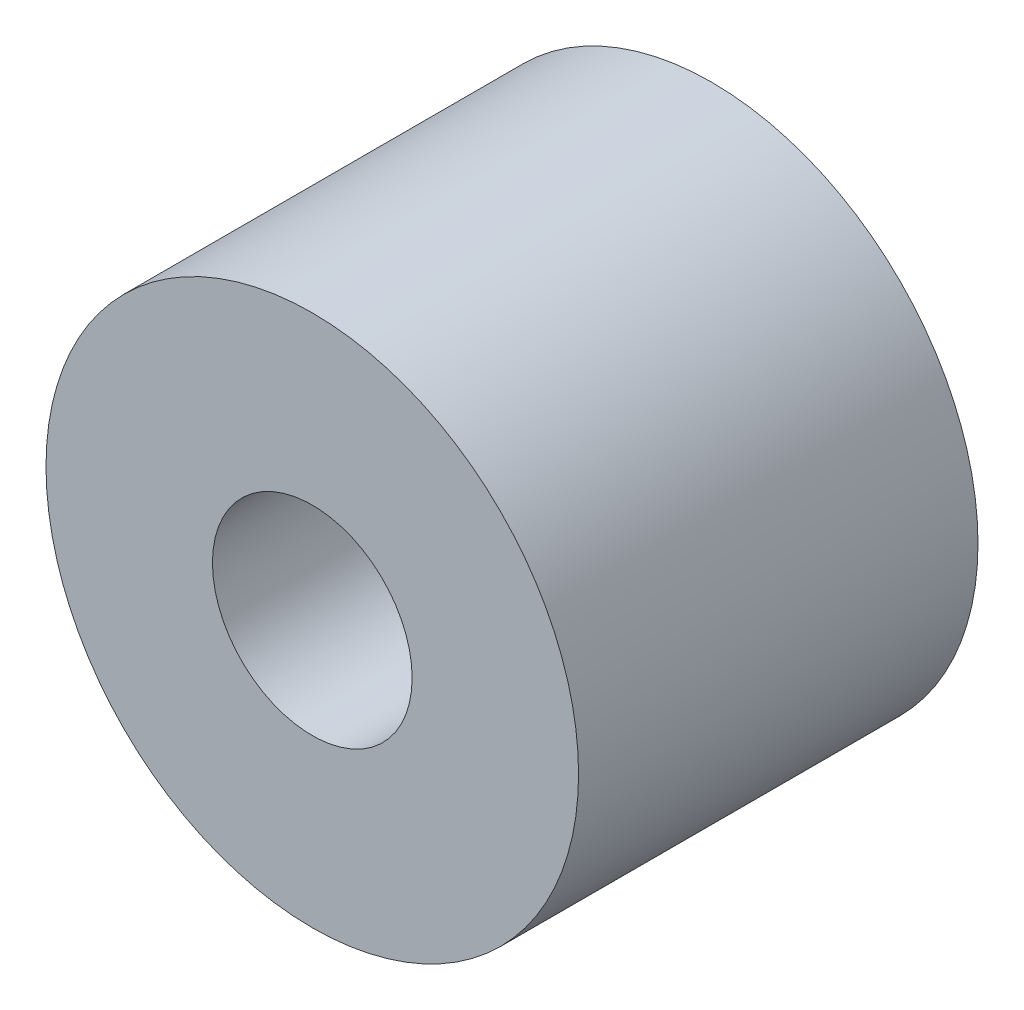
SolidWorks part; units mm, degrees
ref_plane "Front Plane" through (0, 0, 0) normal (0, 0, 1) x (1, 0, 0)
ref_plane "Top Plane" through (0, 0, 0) normal (0, 1, 0) x (1, 0, 0)
ref_plane "Right Plane" through (0, 0, 0) normal (1, 0, 0) x (0, 0, -1)
sketch "Sketch1" plane through (0, 0, 0) normal (0, 0, 1) x (1, 0, 0)
  circle A0 centre (0, 0) radius 22.5
  circle A1 centre (0, 0) radius 60
  dimension "D1" = 45
  dimension "D2" = 120
extrude "Boss-Extrude1" add sketch "Sketch1" along normal blind 90
